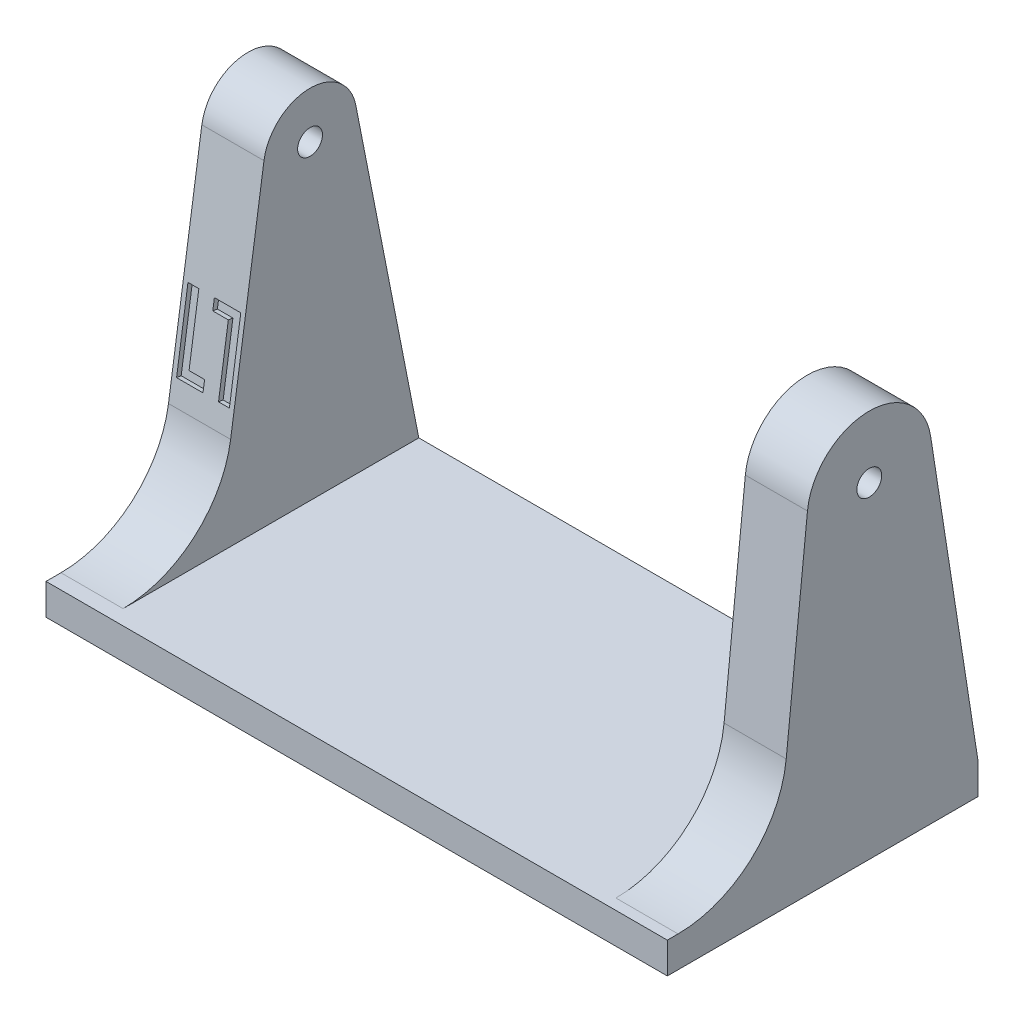
SolidWorks part; units mm, degrees
other "Marca1"
sketch "Croquis12" plane through (-17.425, 25, -10) normal (-0.0042, 0.2203, -0.9754) x (-1, 0, 0.0043)
ref_plane "Alzado" through (0, 0, 0) normal (0, 0, 1) x (1, 0, 0)
ref_plane "Planta" through (0, 0, 0) normal (0, 1, 0) x (1, 0, 0)
ref_plane "Vista lateral" through (0, 0, 0) normal (1, 0, 0) x (0, 0, -1)
sketch "Croquis1" plane through (0, 0, 0) normal (0, 1, 0) x (1, 0, 0)
  line L1 (-20, 10) -> (20, 10)
  line L2 (-20, 10) -> (-20, -10)
  line L3 (-20, -10) -> (20, -10)
  line L4 (20, 10) -> (20, -10)
  line L5 (-20, 10) -> (20, -10) construction
  line L6 (-20, -10) -> (20, 10) construction
  point P0 (0, 0)
  dimension "D1" = 20
  dimension "D2" = 40
extrude "Saliente-Extruir1" add sketch "Croquis1" along normal blind 2
sketch "Croquis3" plane through (20, 0, 0) normal (1, 0, 0) x (0, 0, -1)
  line L0 (-10, 2) -> (-9.309, 2) construction
  line L1 (-10, 2) -> (10, 2) construction
  line L2 (-2.3466, 8.275) -> (-0.9785, 21.4143)
  line L3 (-9.309, 2) -> (10, 2)
  line L4 (-10, 0) -> (10, 0) construction
  line L5 (10, 2) -> (6.9526, 21.6141)
  circle A0 centre (3, 21) radius 0.8
  arc A1 (6.9526, 21.6141) -> (-0.9785, 21.4143) centre (3, 21) ccw
  arc A2 (-9.309, 2) -> (-2.3466, 8.275) centre (-9.309, 9) ccw
  point P18 (-3, 2)
  dimension "D1" = 1.6
  dimension "D2" = 8
  dimension "D6" = 7
  dimension "D3" = 7
  dimension "D4" = 21
  dimension "D5" = 3
extrude "Saliente-Extruir2" add sketch "Croquis3" against normal blind 4
sketch "Croquis4" plane through (0, 0, 0) normal (0, -1, 0) x (1, 0, 0)
  line L0 (0, 13.0259) -> (0, -14.9102) construction
  line L3 (0, 8) -> (0, 6) construction
  line L6 (0.5, 8) -> (0.5, 6)
  line L9 (-0.5, 8) -> (-0.5, 6)
  line L10 (19.4819, 7) -> (-19.3961, 7) construction
  line L12 (2, 8) -> (2, 6)
  line L13 (3, 8) -> (3, 6)
  line L14 (2.5, 8) -> (2.5, 6) construction
  line L15 (4.5, 8) -> (4.5, 6)
  line L16 (5.5, 8) -> (5.5, 6)
  line L17 (5, 8) -> (5, 6) construction
  line L18 (7, 8) -> (7, 6)
  line L19 (8, 8) -> (8, 6)
  line L20 (7.5, 8) -> (7.5, 6) construction
  line L21 (9.5, 8) -> (9.5, 6)
  line L22 (10.5, 8) -> (10.5, 6)
  line L23 (10, 8) -> (10, 6) construction
  line L24 (12, 8) -> (12, 6)
  line L25 (13, 8) -> (13, 6)
  line L26 (12.5, 8) -> (12.5, 6) construction
  line L27 (-0.5, 8) -> (2, 8) construction
  circle A15 centre (7, -5) radius 2.5
  circle A16 centre (7, -5) radius 1
  arc A17 (0.5, 8) -> (-0.5, 8) centre (0, 8) ccw
  arc A18 (-0.5, 6) -> (0.5, 6) centre (0, 6) ccw
  arc A19 (3, 8) -> (2, 8) centre (2.5, 8) ccw
  arc A20 (2, 6) -> (3, 6) centre (2.5, 6) ccw
  arc A21 (5.5, 8) -> (4.5, 8) centre (5, 8) ccw
  arc A22 (4.5, 6) -> (5.5, 6) centre (5, 6) ccw
  arc A23 (8, 8) -> (7, 8) centre (7.5, 8) ccw
  arc A24 (7, 6) -> (8, 6) centre (7.5, 6) ccw
  arc A25 (10.5, 8) -> (9.5, 8) centre (10, 8) ccw
  arc A26 (9.5, 6) -> (10.5, 6) centre (10, 6) ccw
  arc A27 (13, 8) -> (12, 8) centre (12.5, 8) ccw
  arc A28 (12, 6) -> (13, 6) centre (12.5, 6) ccw
  point P8 (0, 7)
  point P17 (2.5, 7)
  point P24 (5, 7)
  point P31 (7.5, 7)
  point P38 (10, 7)
  point P45 (12.5, 7)
  dimension "D1" = 2
  dimension "D2" = 5
  dimension "D3" = 5
  dimension "D4" = 7
  dimension "D5" = 2
  dimension "D6" = 0.5
  dimension "D7" = 6
  dimension "D8" = 2.5
extrude "Cortar-Extruir1" cut sketch "Croquis4" against normal blind 0.2
mirror "Simetría2" about plane through (0, 0, 0) normal (1, 0, 0) of "Cortar-Extruir1"
sketch "Croquis6" plane through (-20, 0, 0) normal (-1, 0, 0) x (0, 0, 1)
  line L0 (-10, 2) -> (-5.9434, 22.5802)
  line L1 (-0.0325, 22.4403) -> (2.1139, 7.9727)
  line L4 (-10, 2) -> (10, 2) construction
  line L5 (9.0381, 2) -> (10, 2) construction
  line L6 (-10, 2) -> (9.0381, 2)
  arc A0 (-0.0325, 22.4403) -> (-5.9434, 22.5802) centre (-3, 22) ccw
  arc A1 (2.1139, 7.9727) -> (9.0381, 2) centre (9.0381, 9) ccw
  circle A2 centre (-3, 22) radius 0.8
  point P15 (3, 2)
  dimension "D1" = 6
  dimension "D3" = 7
  dimension "D4" = 1.6
  dimension "D6" = 20.5802
  dimension "D2" = 7
  dimension "D5" = 20
extrude "Saliente-Extruir3" add sketch "Croquis6" against normal blind 4
sketch "Croquis10" plane through (16, 0, 0) normal (-1, 0, 0) x (0, 0, 1)
  circle A0 centre (-3, 21) radius 2.4
  dimension "D1" = 4.8
extrude "Cortar-Extruir4" cut sketch "Croquis10" against normal blind 2
sketch "Croquis11" plane through (0, 0.4786, 3.2257) normal (0, 0.1468, 0.9892) x (1, 0, 0)
  line L0 (-16.3, 9.0762) -> (-17, 9.0762)
  line L1 (-17, 9.0762) -> (-17, 13.3762)
  line L2 (-17, 13.3762) -> (-18, 13.3762)
  line L3 (-18, 13.3762) -> (-18, 14.0762)
  line L4 (-18, 14.0762) -> (-16.3, 14.0762)
  line L5 (-16.3, 14.0762) -> (-16.3, 9.0762)
  line L6 (-18, 14.5762) -> (-18, 8.5762) construction
  line L7 (-18.8787, 11.5762) -> (-17.1213, 11.5762) construction
  line L8 (-16, 7.5762) -> (-16, 22.2021) construction
  line L9 (-16, 7.5762) -> (-20, 7.5762) construction
  line L10 (-19.7, 9.0762) -> (-19.7, 14.0762)
  line L11 (-19.7, 14.0762) -> (-19, 14.0762)
  line L12 (-19, 14.0762) -> (-19, 9.7762)
  line L13 (-19, 9.7762) -> (-18, 9.7762)
  line L14 (-18, 9.7762) -> (-18, 9.0762)
  line L15 (-18, 9.0762) -> (-19.7, 9.0762)
  point P13 (-16.3, 11.5762)
  point P16 (-19.7, 11.5762)
  point P17 (-18, 11.5762)
  point P24 (-18, 11.5762)
  dimension "D1" = 5
  dimension "D2" = 0.7
  dimension "D3" = 0.7
  dimension "D4" = 1
  dimension "D5" = 2
  dimension "D6" = 6
  dimension "D7" = 4
  dimension "D8" = 2
extrude "Cortar-Extruir5" cut sketch "Croquis11" against normal blind 0.3
